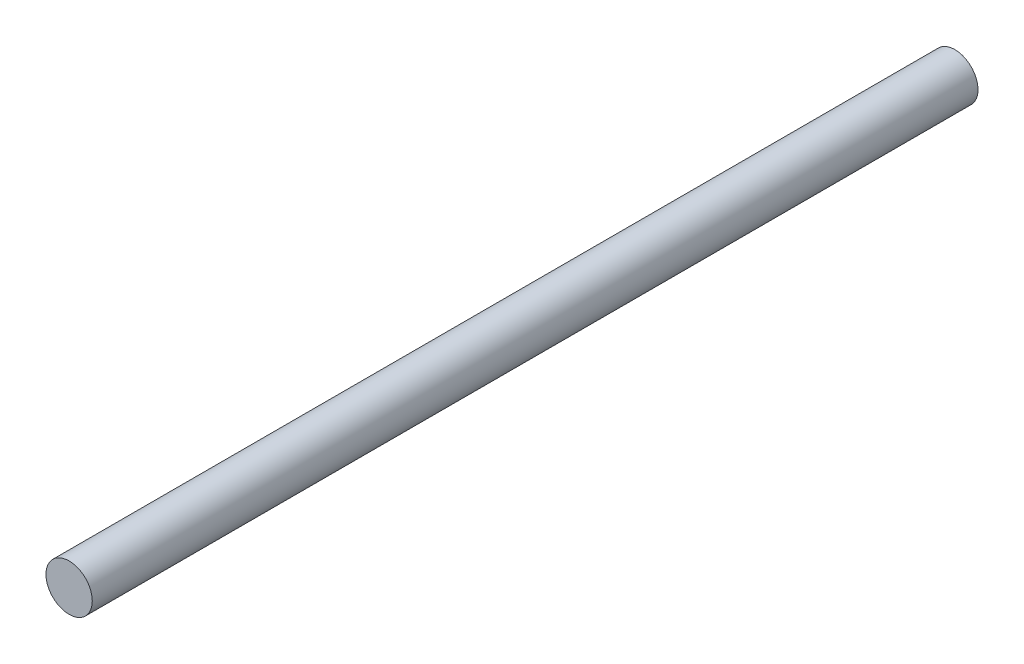
SolidWorks part; units mm, degrees
ref_plane "Front Plane" through (0, 0, 0) normal (0, 0, 1) x (1, 0, 0)
ref_plane "Top Plane" through (0, 0, 0) normal (0, 1, 0) x (1, 0, 0)
ref_plane "Right Plane" through (0, 0, 0) normal (1, 0, 0) x (0, 0, -1)
sketch "Sketch1" plane through (0, 0, 0) normal (0, 0, 1) x (1, 0, 0)
  circle A0 centre (0, 0) radius 4
  dimension "D1" = 8
extrude "Boss-Extrude1" add sketch "Sketch1" along normal blind 153
